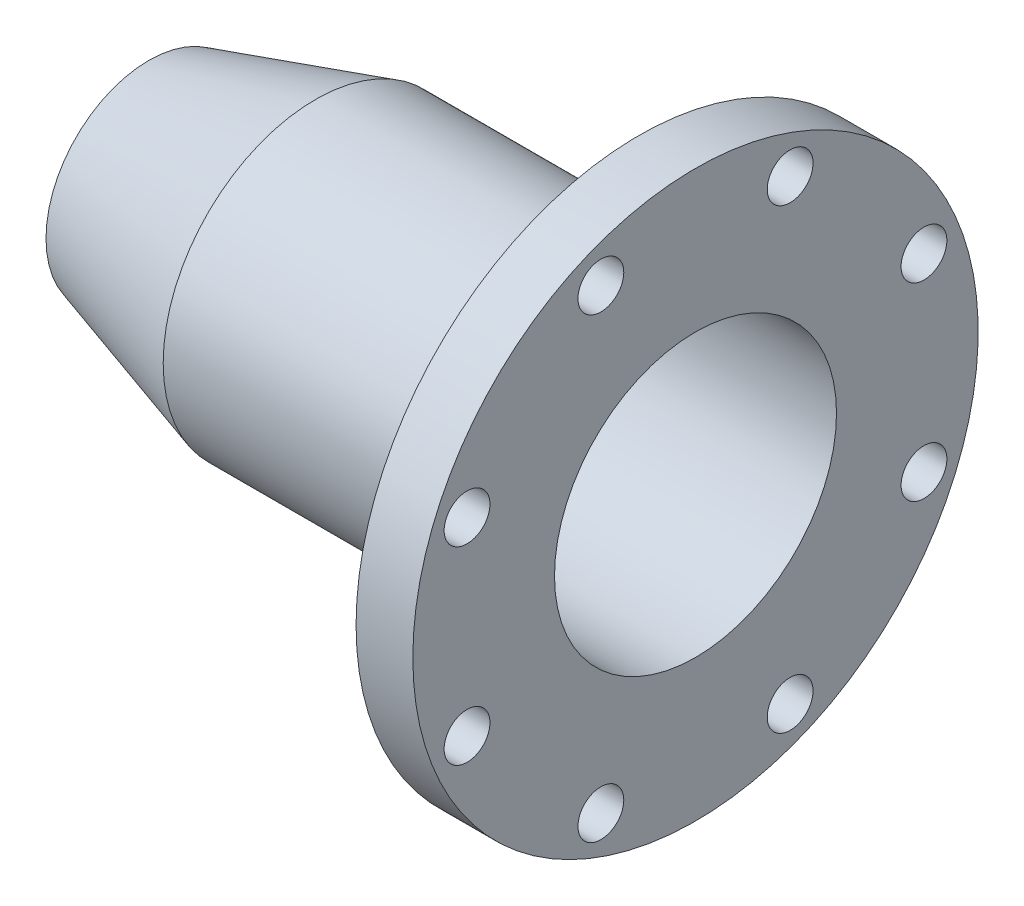
SolidWorks part; units mm, degrees
other "Camera1"
material "PP Homopolymer"
ref_plane "Front Plane" through (0, 0, 0) normal (0, 0, 1) x (1, 0, 0)
ref_plane "Top Plane" through (0, 0, 0) normal (0, 1, 0) x (1, 0, 0)
ref_plane "Right Plane" through (0, 0, 0) normal (1, 0, 0) x (0, 0, -1)
sketch "Sketch1" plane through (0, 0, 0) normal (0, 0, 1) x (1, 0, 0)
  line L0 (0, 0) -> (541.4119, 0) construction
  line L1 (266.7, 68.795) -> (266.7, 137.92)
  line L2 (266.7, 137.92) -> (239.01, 137.92)
  line L3 (239.01, 137.92) -> (239.01, 74.295)
  line L4 (239.01, 74.295) -> (81.28, 74.295)
  line L5 (239.01, 68.795) -> (82.0785, 68.795)
  line L6 (239.01, 68.795) -> (266.7, 68.795)
  line L7 (81.28, 74.295) -> (0, 50.1868)
  line L8 (82.0785, 68.795) -> (0, 44.45)
  line L9 (0, 50.1868) -> (0, 44.45)
  line L10 (239.01, 74.295) -> (266.7, 74.295)
  dimension "D2" = 27.69
  dimension "D3" = 74.295
  dimension "D4" = 185.42
  dimension "D5" = 266.7
  dimension "D6" = 5.5
  dimension "D7" = 5.5
  dimension "D1" = 44.45
revolve "Revolve1" add sketch "Sketch1" angle 360 about L0
sketch "Sketch3" plane through (266.7, 0, 0) normal (1, 0, 0) x (0, 0, -1)
  line L0 (0, 0) -> (0, 120.65) construction
  line L1 (0, 0) -> (-46.1708, 111.4661) construction
  circle A0 centre (0, 0) radius 120.65 construction
  dimension "D1" = 241.3
  dimension "D2" = 22.5
hole_wizard "7/8 (0.88) Diameter Hole1" positions "3DSketch2" profile "Sketch7" hole size "7/8" standard "ANSI Inch" end condition through all
sketch3d "3DSketch2"
  point P0 (266.7, 111.4661, 46.1708)
sketch "Sketch7" plane through (266.7, 111.4661, 46.1708) normal (0, 1, 0) x (0, 0, -1)
  line L0 (0, 0) -> (0, 266.7)
  line L1 (0, 266.7) -> (11.176, 266.7)
  line L2 (11.176, 266.7) -> (11.176, 0)
  line L5 (11.176, 0) -> (0, 0)
  line L11 (0, -6.35) -> (0, 107.95) construction
  dimension "Thru Hole Dia." = 22.352
  dimension "Thru Hole Depth" = 266.7
pattern_circular "CirPattern1" count 8 over 360 about axis through (0, 0, 0) along (1, 0, 0) of "7/8 (0.88) Diameter Hole1"
equation "\"Wall Thickness\"= 5.5"
equation "\"D6@Sketch1\"=\"Wall Thickness\""
equation "\"Nozzle diameter\"= 3.5 * 25.4"
equation "\"D7@Sketch1\"=\"Wall Thickness\""
equation "\"D1@Sketch1\"=\"Nozzle diameter\"/2"
